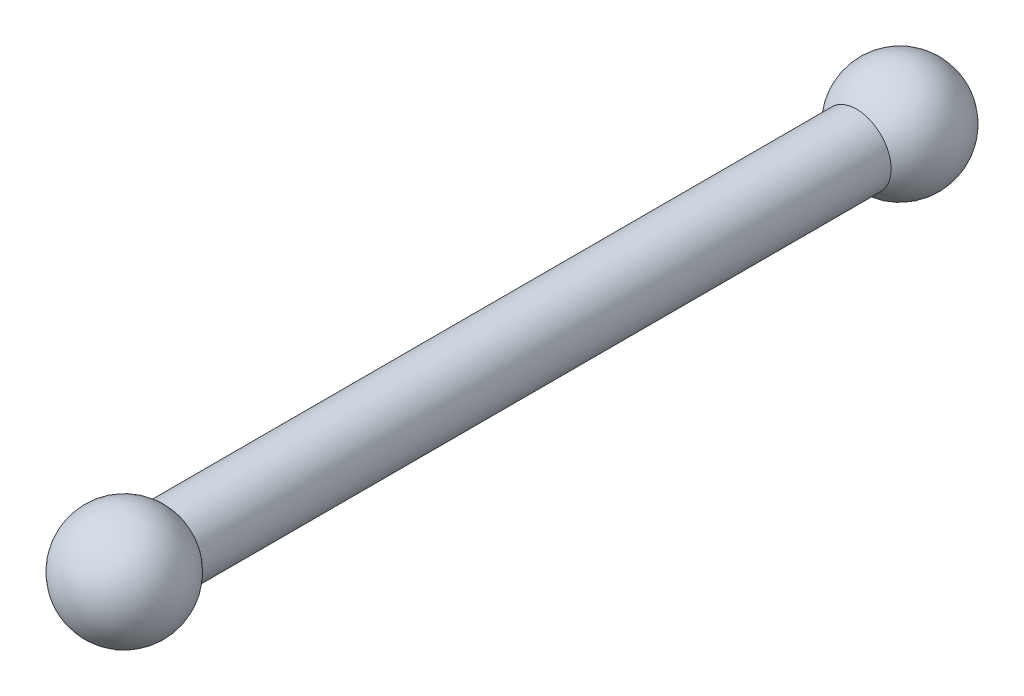
SolidWorks part; units mm, degrees
ref_plane "Front Plane" through (0, 0, 0) normal (0, 0, 1) x (1, 0, 0)
ref_plane "Top Plane" through (0, 0, 0) normal (0, 1, 0) x (1, 0, 0)
ref_plane "Right Plane" through (0, 0, 0) normal (1, 0, 0) x (0, 0, -1)
sketch "Sketch1" plane through (0, 0, 0) normal (1, 0, 0) x (0, 0, -1)
  line L0 (-12.7, 0) -> (190.5, 0) construction
  line L1 (9.9139, 7.9375) -> (167.8861, 7.9375)
  line L2 (10.9317, 6.4643) -> (166.8683, 6.4643)
  line L3 (165.1, 0) -> (190.5, 0)
  line L4 (-12.7, 0) -> (12.7, 0)
  arc A0 (190.5, 0) -> (167.8861, 7.9375) centre (177.8, 0) ccw
  arc A1 (12.7, 0) -> (10.9317, 6.4643) centre (0, 0) ccw
  arc A2 (9.9139, 7.9375) -> (-12.7, 0) centre (0, 0) ccw
  arc A3 (166.8683, 6.4643) -> (165.1, 0) centre (177.8, 0) ccw
  dimension "D1" = 25.4
  dimension "D2" = 1.4732
  dimension "D3" = 7.9375
  dimension "D4" = 177.8
revolve "Revolve5" add sketch "Sketch1" angle 360 about L0
